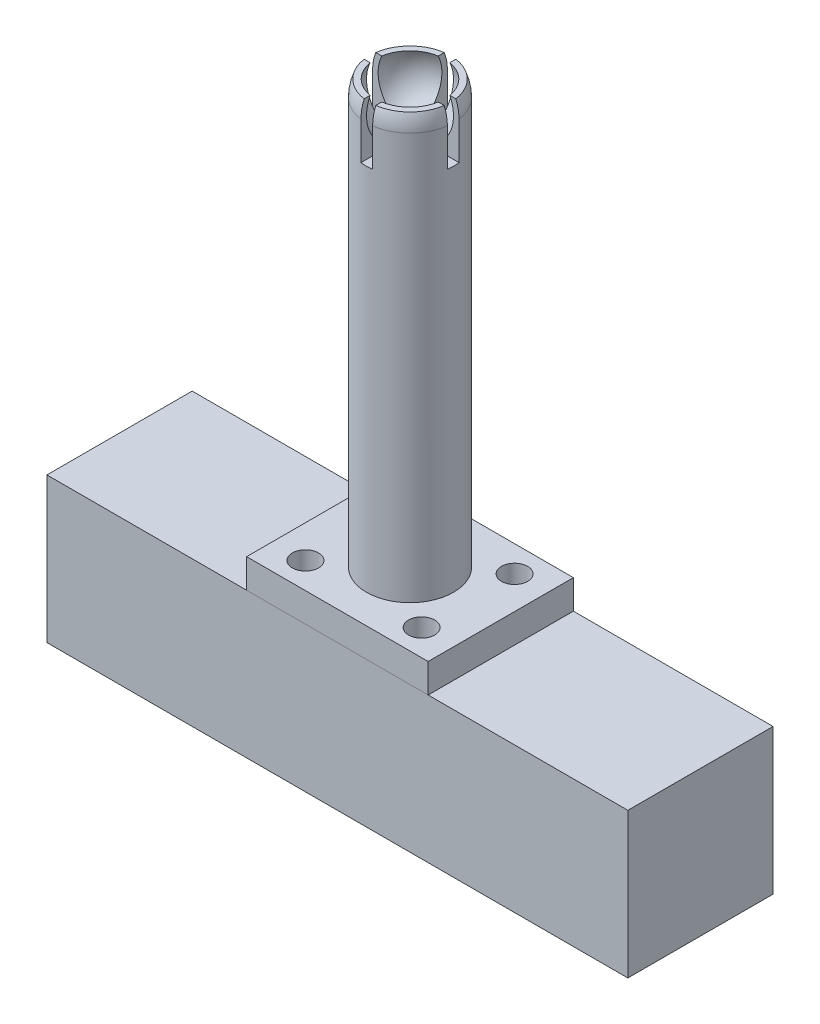
SolidWorks part; units mm, degrees
ref_plane "Front Plane" through (0, 0, 0) normal (0, 0, 1) x (1, 0, 0)
ref_plane "Top Plane" through (0, 0, 0) normal (0, 1, 0) x (1, 0, 0)
ref_plane "Right Plane" through (0, 0, 0) normal (1, 0, 0) x (0, 0, -1)
sketch "Sketch1" plane through (0, 0, 0) normal (0, 1, 0) x (1, 0, 0)
  line L1 (-50.8, 12.7) -> (50.8, 12.7)
  line L2 (-50.8, 12.7) -> (-50.8, -12.7)
  line L3 (-50.8, -12.7) -> (50.8, -12.7)
  line L4 (50.8, 12.7) -> (50.8, -12.7)
  line L5 (-50.8, 12.7) -> (50.8, -12.7) construction
  line L6 (-50.8, -12.7) -> (50.8, 12.7) construction
  point P0 (0, 0)
  dimension "D1" = 101.6
  dimension "D2" = 25.4
extrude "Boss-Extrude1" add sketch "Sketch1" along normal blind 25.4
sketch "Sketch2" plane through (0, 25.4, 0) normal (0, 1, 0) x (1, 0, 0)
  line L0 (-50.8, -12.7) -> (50.8, -12.7) construction
  line L1 (-15.875, 12.7) -> (15.875, 12.7)
  line L2 (-15.875, 12.7) -> (-15.875, -12.7)
  line L3 (-15.875, -12.7) -> (15.875, -12.7)
  line L4 (15.875, 12.7) -> (15.875, -12.7)
  line L5 (-15.875, 12.7) -> (15.875, -12.7) construction
  line L6 (-15.875, -12.7) -> (15.875, 12.7) construction
  circle A0 centre (10.16, -8.128) radius 2.286
  circle A1 centre (-10.16, -8.128) radius 2.286
  circle A2 centre (-10.16, 8.128) radius 2.286
  circle A3 centre (10.16, 8.128) radius 2.286
  point P0 (0, 0)
  dimension "D2" = 4.572
  dimension "D1" = 31.75
  dimension "D3" = 10.16
extrude "Boss-Extrude2" add sketch "Sketch2" along normal blind 5.08 separate body
sketch "Sketch3" plane through (0, 30.48, 0) normal (0, 1, 0) x (1, 0, 0)
  circle A0 centre (0, 0) radius 7.62
  dimension "D1" = 15.24
extrude "Boss-Extrude3" add sketch "Sketch3" along normal blind 63.5
sketch "Sketch4" plane through (0, 0, 0) normal (0, 0, 1) x (1, 0, 0)
  line L0 (7.62, 93.98) -> (-7.62, 93.98) construction
  line L1 (7.62, 93.98) -> (-7.62, 93.98)
  line L2 (-7.62, 93.98) -> (-7.62, 101.6)
  line L4 (0, 93.98) -> (0, 94.9325)
  line L5 (-6.0428, 104.4178) -> (-6.9061, 104.8204)
  line L6 (-6.0428, 104.4178) -> (0, 101.6) construction
  line L7 (-6.0428, 104.4178) -> (-7.0799, 104.4178)
  arc A0 (-6.9061, 104.8204) -> (-7.62, 101.6) centre (0, 101.6) ccw
  arc A1 (-6.0428, 104.4178) -> (0, 94.9325) centre (0, 101.6) ccw
  point P6 (0, 93.98)
  dimension "D1" = 15.24
  dimension "D2" = 13.335
  dimension "D3" = 65
revolve "Revolve1" add sketch "Sketch4" angle 360 about axis through (0, 93.98, 0) along (0, -1, 0)
ref_plane "Plane1" through (0, 104.4178, 0) normal (0, 1, 0) x (1, 0, 0)
sketch "Sketch5" plane through (0, 104.4178, 0) normal (0, 1, 0) x (1, 0, 0)
  line L1 (8.89, -1.016) -> (-8.89, -1.016)
  line L2 (8.89, -1.016) -> (8.89, 1.016)
  line L3 (8.89, 1.016) -> (-8.89, 1.016)
  line L4 (-8.89, -1.016) -> (-8.89, 1.016)
  line L5 (8.89, -1.016) -> (-8.89, 1.016) construction
  line L6 (8.89, 1.016) -> (-8.89, -1.016) construction
  line L7 (1.016, 8.89) -> (-1.016, 8.89)
  line L8 (1.016, 8.89) -> (1.016, -8.89)
  line L9 (1.016, -8.89) -> (-1.016, -8.89)
  line L10 (-1.016, 8.89) -> (-1.016, -8.89)
  line L11 (1.016, 8.89) -> (-1.016, -8.89) construction
  line L12 (1.016, -8.89) -> (-1.016, 8.89) construction
  point P0 (0, 0)
  point P6 (0, 0)
  dimension "D1" = 17.78
  dimension "D2" = 2.032
extrude "Cut-Extrude2" cut sketch "Sketch5" against normal blind 9.398 contours L1 L10 L9 L8 | L7 L10 L3 L8 | L3 L8 L1 L2 | L10 L3 L4 L1 | L3 L10 L1 L8
